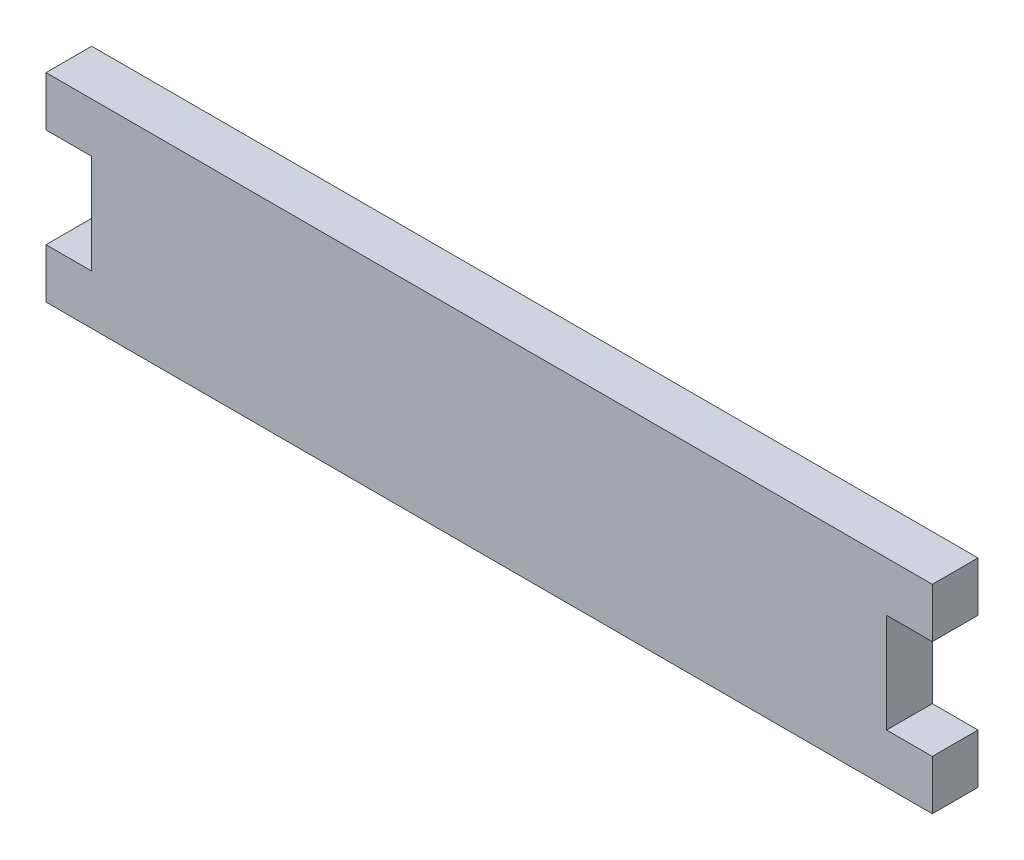
SolidWorks part; units mm, degrees
ref_plane "Front Plane" through (0, 0, 0) normal (0, 0, 1) x (1, 0, 0)
ref_plane "Top Plane" through (0, 0, 0) normal (0, 1, 0) x (1, 0, 0)
ref_plane "Right Plane" through (0, 0, 0) normal (1, 0, 0) x (0, 0, -1)
sketch "Sketch1" plane through (0, 0, 0) normal (0, 0, 1) x (1, 0, 0)
  line L0 (-50.8, 0) -> (50.8, 0) construction
  line L1 (50.8, -12.7) -> (-50.8, -12.7)
  line L2 (50.8, -6.35) -> (50.8, 6.35)
  line L3 (50.8, 12.7) -> (-50.8, 12.7)
  line L4 (-50.8, -6.35) -> (-50.8, 6.35)
  line L5 (50.8, -12.7) -> (-50.8, 12.7) construction
  line L6 (50.8, 12.7) -> (-50.8, -12.7) construction
  line L7 (-56.642, -12.7) -> (-50.8, -6.35) construction
  line L8 (-56.642, 6.35) -> (-50.8, 6.35)
  line L9 (-56.642, 6.35) -> (-56.642, 12.7)
  line L10 (-56.642, 12.7) -> (-50.8, 12.7)
  line L11 (0, 12.7) -> (0, -12.7) construction
  line L12 (-56.642, 6.35) -> (-50.8, 12.7) construction
  line L13 (-56.642, 12.7) -> (-50.8, 6.35) construction
  line L14 (-56.642, -6.35) -> (-50.8, -12.7) construction
  line L15 (56.642, -6.35) -> (50.8, -12.7) construction
  line L16 (-56.642, -12.7) -> (-50.8, -12.7)
  line L17 (-56.642, -6.35) -> (-56.642, -12.7)
  line L18 (-56.642, -6.35) -> (-50.8, -6.35)
  line L19 (56.642, 12.7) -> (50.8, 6.35) construction
  line L20 (56.642, 6.35) -> (50.8, 12.7) construction
  line L21 (56.642, -12.7) -> (50.8, -6.35) construction
  line L22 (56.642, -6.35) -> (50.8, -6.35)
  line L23 (56.642, -6.35) -> (56.642, -12.7)
  line L24 (56.642, -12.7) -> (50.8, -12.7)
  line L25 (56.642, 12.7) -> (50.8, 12.7)
  line L26 (56.642, 6.35) -> (56.642, 12.7)
  line L27 (56.642, 6.35) -> (50.8, 6.35)
  line L28 (50.8, -6.35) -> (50.8, 6.35)
  point P0 (0, 0)
  point P8 (-53.721, 9.525)
  point P15 (-53.721, -9.525)
  point P24 (53.721, -9.525)
  point P25 (53.721, 9.525)
  dimension "D1" = 101.6
  dimension "D2" = 25.4
  dimension "D3" = 6.35
  dimension "D4" = 5.842
extrude "Boss-Extrude1" add sketch "Sketch1" along normal blind 5.842 contours L27 L26 L25 L3 L10 L9 L8 L4 L18 L17 L16 L1 L24 L23 L22 L2
